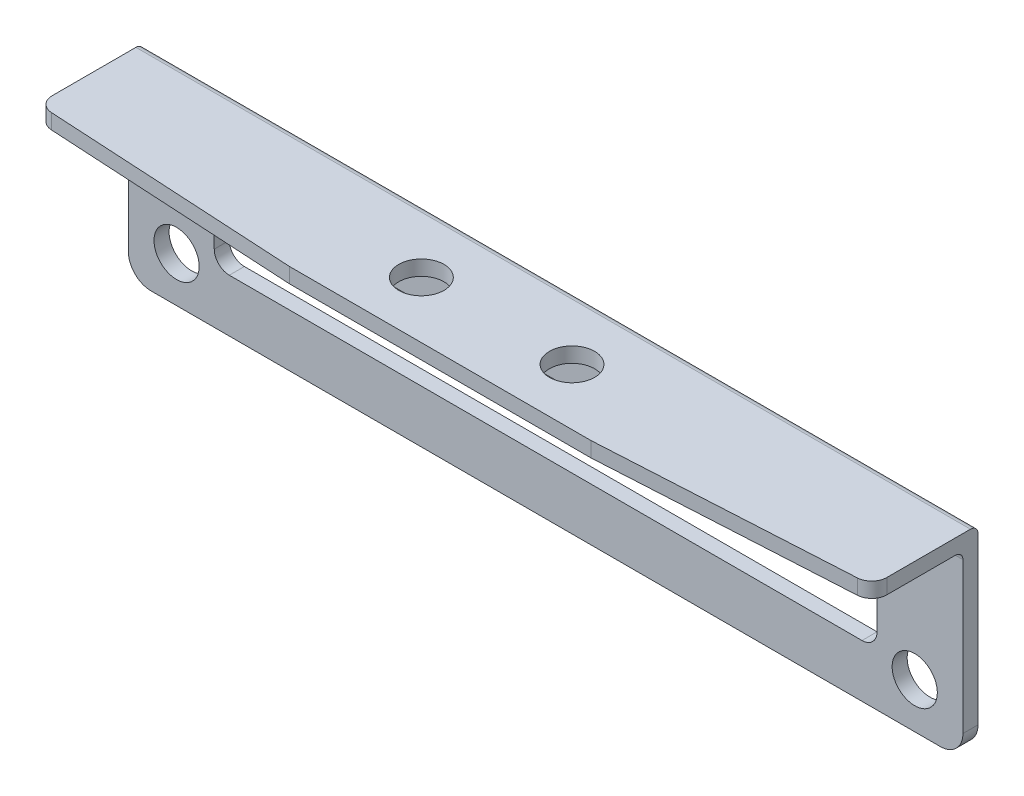
SolidWorks part; units mm, degrees
ref_plane "前视基准面" through (0, 0, 0) normal (0, 0, 1) x (1, 0, 0)
ref_plane "上视基准面" through (0, 0, 0) normal (0, 1, 0) x (1, 0, 0)
ref_plane "右视基准面" through (0, 0, 0) normal (1, 0, 0) x (0, 0, -1)
sketch "草图1" plane through (0, 0, 0) normal (0, 0, 1) x (1, 0, 0)
  line L0 (-27.7, 13) -> (-27.7, 0)
  line L1 (-27.7, 0) -> (27.7, 0)
  line L2 (27.7, 0) -> (27.7, 13)
  line L3 (27.7, 13) -> (-27.7, 13)
  line L5 (-22, 8.3) -> (22, 8.3)
  line L6 (-22, 8.3) -> (-22, 3.5)
  line L7 (0, 0) -> (0, 14.9169) construction
  line L8 (-22, 3.5) -> (22, 3.5)
  line L9 (22, 8.3) -> (22, 3.5)
  line L10 (-22, 8.3) -> (22, 3.5) construction
  line L11 (-22, 3.5) -> (22, 8.3) construction
  circle A2 centre (-24.5, 3) radius 1.5
  circle A3 centre (24.5, 3) radius 1.5
  circle A4 centre (-24.5, 3) radius 2.5 construction
  point P2 (0, 5.9)
  dimension "D1" = 3
  dimension "D2" = 3
  dimension "D10" = 5
  dimension "D3" = 49
  dimension "D4" = 10
  dimension "D5" = 55.4
  dimension "D6" = 44
  dimension "D7" = 4.8
  dimension "D8" = 3.5
  dimension "D9" = 13
extrude "凸台-拉伸1" add sketch "草图1" along normal blind 1
sketch "草图2" plane through (0, 0, 1) normal (0, 0, 1) x (1, 0, 0)
  line L0 (27.7, 13) -> (-27.7, 13) construction
  line L1 (27.7, 13) -> (-27.7, 13)
  line L2 (27.7, 12) -> (-27.7, 12)
  line L3 (-27.7, 13) -> (-27.7, 12)
  line L4 (27.7, 13) -> (27.7, 12)
  dimension "D1" = 1
extrude "凸台-拉伸2" add sketch "草图2" along normal blind 7
sketch "草图3" plane through (0, 12, 0) normal (0, -1, 0) x (1, 0, 0)
  line L0 (-27.7, 8) -> (-27.7, 1) construction
  line L1 (27.7, 8) -> (27.7, 1) construction
  line L2 (-27.7, 8) -> (-27.7, 7)
  line L3 (27.7, 8) -> (27.7, 7)
  line L4 (-10, 8) -> (-27.7, 7)
  line L5 (-27.7, 8) -> (27.7, 8) construction
  line L6 (0, 0) -> (0, 16.8501) construction
  line L7 (10, 8) -> (27.7, 7)
  line L8 (-27.7, 8) -> (-10, 8)
  line L9 (10, 8) -> (27.7, 8)
  line L10 (-27.7, 1) -> (27.7, 1) construction
  dimension "D1" = 20
  dimension "D2" = 6
extrude "切除-拉伸1" cut sketch "草图3" against normal through all
sketch "草图4" plane through (0, 12, 0) normal (0, -1, 0) x (1, 0, 0)
  line L0 (-14.9845, 4.25) -> (10.8142, 4.25) construction
  line L1 (-10, 8) -> (10, 8) construction
  line L2 (0, 0) -> (0, 12.2171) construction
  circle A0 centre (-5, 4.25) radius 1.5
  circle A1 centre (5, 4.25) radius 1.5
  dimension "D3" = 3
  dimension "D4" = 3
  dimension "D1" = 3.75
  dimension "D2" = 10
extrude "切除-拉伸2" cut sketch "草图4" against normal through all
fillet "圆角1" radius 0.5 2 edges at (0, 13, 0)
fillet "圆角2" radius 1 4 edges at (22, 3.5, 0.5) (22, 8.3, 0.5) (-22, 3.5, 0.5) (-22, 8.3, 0.5)
fillet "圆角3" radius 1.5 2 edges at (27.7, 0, 0.5) (-27.7, 0, 0.5)
fillet "圆角4" radius 1 2 edges at (-27.7, 12.5, 7) (27.7, 12.5, 7)
